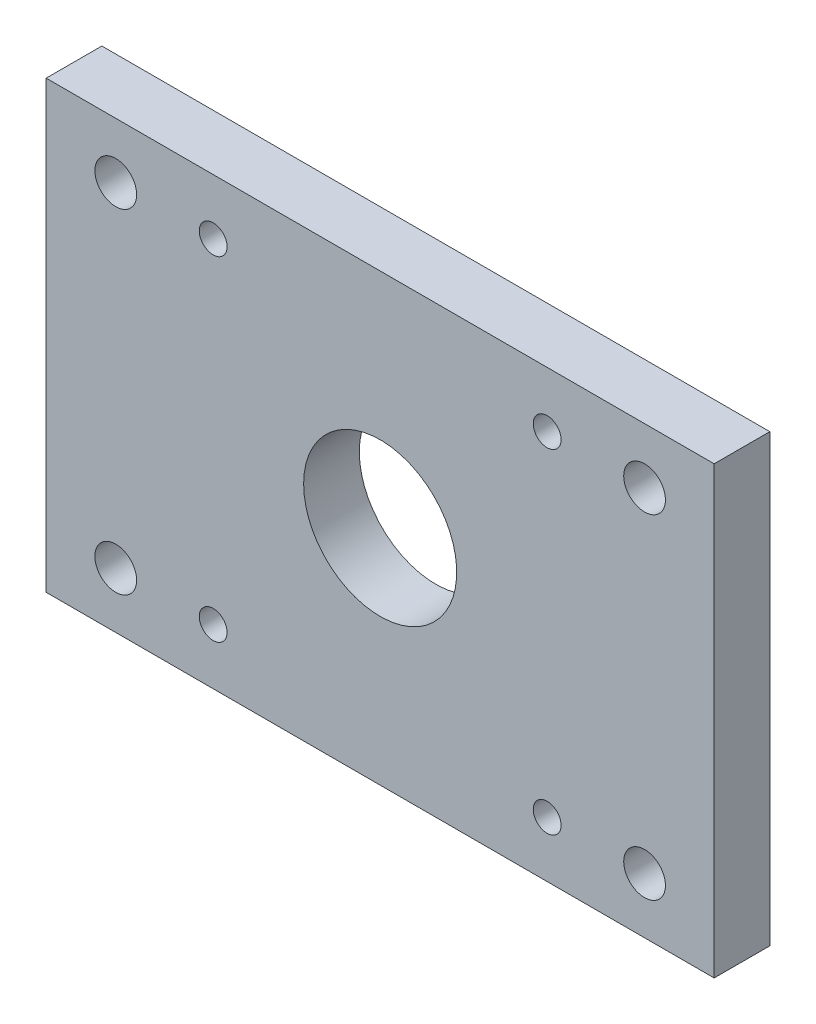
SolidWorks part; units mm, degrees
ref_plane "Front Plane" through (0, 0, 0) normal (0, 0, 1) x (1, 0, 0)
ref_plane "Top Plane" through (0, 0, 0) normal (0, 1, 0) x (1, 0, 0)
ref_plane "Right Plane" through (0, 0, 0) normal (1, 0, 0) x (0, 0, -1)
sketch "Sketch1" plane through (0, 0, 0) normal (0, 0, 1) x (1, 0, 0)
  line L1 (0, 0) -> (76.2, 0)
  line L2 (0, 0) -> (0, 50.8)
  line L3 (0, 50.8) -> (76.2, 50.8)
  line L4 (76.2, 0) -> (76.2, 50.8)
  dimension "D1" = 50.8
  dimension "D2" = 76.2
extrude "Boss-Extrude1" add sketch "Sketch1" along normal blind 6.35
sketch "Sketch2" plane through (0, 0, 0) normal (0, 0, -1) x (-1, 0, 0)
  line L0 (0, 25.4) -> (-76.2, 25.4) construction
  line L1 (0, 50.8) -> (0, 0) construction
  line L2 (-76.2, 0) -> (-76.2, 50.8) construction
  line L3 (-38.1, 50.8) -> (-38.1, 0) construction
  line L4 (-76.2, 50.8) -> (0, 50.8) construction
  line L5 (0, 0) -> (-76.2, 0) construction
  circle A0 centre (-38.1, 25.4) radius 8.7313
  dimension "D1" = 17.4625
sketch "Sketch3" plane through (0, 0, 0) normal (0, 0, -1) x (-1, 0, 0)
  line L0 (-76.2, 0) -> (-76.2, 50.8) construction
  line L1 (-76.2, 50.8) -> (0, 50.8) construction
  circle A0 centre (-68.2625, 44.45) radius 2.3813
  dimension "D1" = 4.7625
  dimension "D2" = 7.9375
  dimension "D3" = 6.35
extrude "Cut-Extrude6" cut sketch "Sketch3" against normal through all
sketch "Sketch4" plane through (0, 0, 0) normal (0, 0, -1) x (-1, 0, 0)
  line L0 (-38.1, 50.8) -> (-38.1, 0) construction
  line L1 (-76.2, 50.8) -> (0, 50.8) construction
  line L2 (0, 0) -> (-76.2, 0) construction
  line L3 (-76.2, 25.4) -> (0, 25.4) construction
  line L4 (-76.2, 0) -> (-76.2, 50.8) construction
  line L5 (0, 50.8) -> (0, 0) construction
ref_plane "Plane1" through (38.1, 0, 0) normal (1, 0, 0) x (0, -1, 0)
mirror "Mirror1" about plane through (38.1, 0, 0) normal (1, 0, 0) of "Cut-Extrude6"
ref_plane "Plane2" through (0, 25.4, 0) normal (0, -1, 0) x (-1, 0, 0)
mirror "Mirror2" about plane through (0, 25.4, 0) normal (0, -1, 0) of "Mirror1", "Cut-Extrude6"
extrude "Cut-Extrude7" cut sketch "Sketch2" against normal through all contours A0
sketch "Sketch5" plane through (0, 0, 0) normal (0, 0, -1) x (-1, 0, 0)
  circle A0 centre (-19.05, 44.45) radius 1.5875
  circle A1 centre (-19.05, 6.35) radius 1.5875
  circle A2 centre (-57.15, 44.45) radius 1.5875
  circle A3 centre (-57.15, 6.35) radius 1.5875
  dimension "D1" = 3.175
  dimension "D2" = 3.175
  dimension "D3" = 3.175
  dimension "D4" = 3.175
extrude "Cut-Extrude8" cut sketch "Sketch5" against normal through all
equation "\"dist\"= 10"
